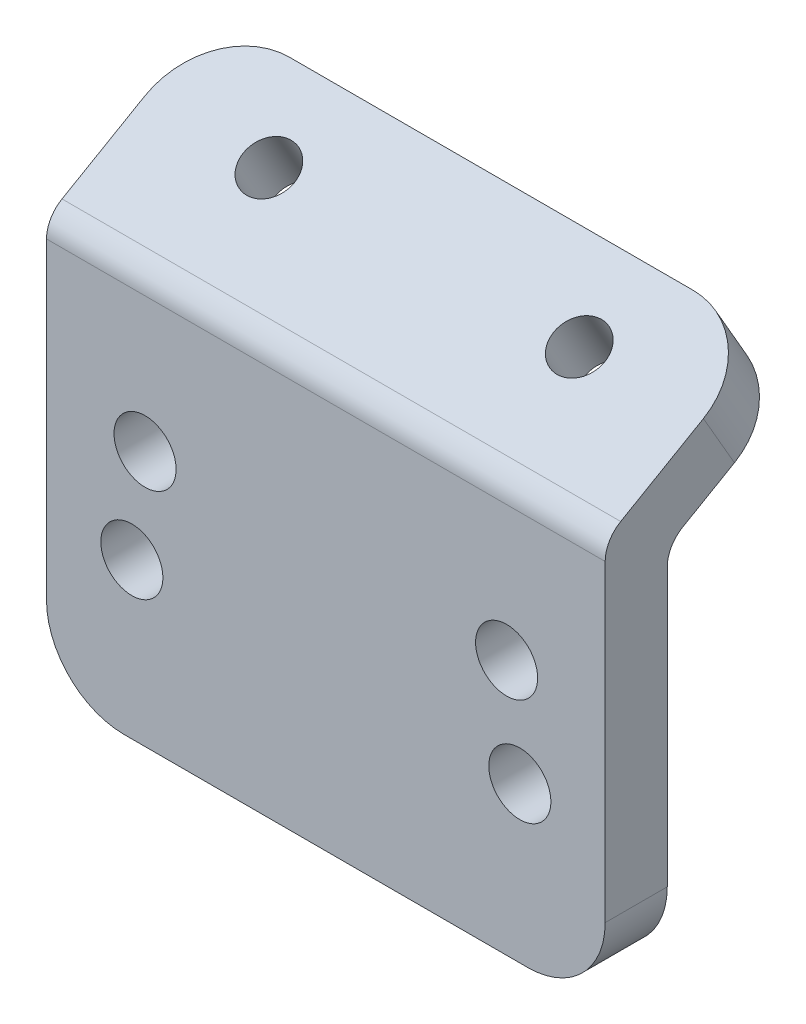
SolidWorks part; units mm, degrees
ref_plane "Plan de face" through (0, 0, 0) normal (0, 0, 1) x (1, 0, 0)
ref_plane "Plan de dessus" through (0, 0, 0) normal (0, 1, 0) x (1, 0, 0)
ref_plane "Plan de droite" through (0, 0, 0) normal (1, 0, 0) x (0, 0, -1)
sketch "Esquisse1" plane through (0, 0, 0) normal (0, 0, 1) x (1, 0, 0)
  line L1 (0, 0) -> (36, 0)
  line L2 (0, 0) -> (0, 24)
  line L3 (0, 24) -> (36, 24)
  line L4 (36, 0) -> (36, 24)
  dimension "D1" = 36
  dimension "D2" = 24
extrude "Boss.-Extru.1" add sketch "Esquisse1" along normal blind 4
sketch "Esquisse2" plane through (0, 0, 4) normal (0, 0, 1) x (1, 0, 0)
  line L0 (18, 0) -> (18, 24) construction
  line L1 (0, 0) -> (36, 0) construction
  line L2 (36, 24) -> (0, 24) construction
  line L3 (5.5, 10) -> (29.6481, 16.4705) construction
  line L4 (5.5, 10) -> (18, 10) construction
  circle A0 centre (5.5, 10) radius 2
  circle A1 centre (30.5, 10) radius 2
  circle A2 centre (29.6481, 16.4705) radius 2
  circle A3 centre (6.3519, 16.4705) radius 2
  dimension "D1" = 25
  dimension "D2" = 10
  dimension "D3" = 4
  dimension "D5" = 25
  dimension "D4" = 15
extrude "Enlèv. mat.-Extru.1" cut sketch "Esquisse2" against normal through all both and the other way through all
sketch "Esquisse3" plane through (36, 0, 0) normal (1, 0, 0) x (0, 0, -1)
  line L0 (0, 24) -> (8.6603, 29)
  line L1 (8.6603, 29) -> (6.6603, 32.4641)
  line L2 (6.6603, 32.4641) -> (-4, 26.3094)
  line L4 (-4, 26.3094) -> (-4, 24)
  line L5 (0, 0) -> (0, 24) construction
  line L6 (0, 24) -> (-4, 24)
  dimension "D1" = 4
  dimension "D2" = 10
  dimension "D3" = 120
extrude "Boss.-Extru.2" add sketch "Esquisse3" against normal up to vertex (36 mm away) up to point (0, 24, 0)
sketch "Esquisse4" plane through (0, 18, 10.3923) normal (0, -0.866, -0.5) x (1, 0, 0)
  line L0 (18, -22) -> (18, -15.2024) construction
  line L1 (0, -22) -> (36, -22) construction
  circle A0 centre (8, -17) radius 1.65
  circle A1 centre (28, -17) radius 1.65
  dimension "D2" = 3.3
  dimension "D3" = 5
  dimension "D1" = 10
extrude "Enlèv. mat.-Extru.2" cut sketch "Esquisse4" against normal through all both and the other way through all
fillet "Congé2" radius 5 4 edges at (0, 30.7321, -7.6603) (36, 30.7321, -7.6603) (0, 0, 2) (36, 0, 2)
fillet "Congé3" radius 2 2 edges at (18, 26.3094, 4) (18, 24, 0)
sketch "Esquisse5" [suppressed] plane through (0, 0, 4) normal (0, 0, 1) x (1, 0, 0)
  line L0 (5.5, 10) -> (29.6481, 16.4705) construction
  line L1 (3.0852, 9.353) -> (7.9148, 10.647) construction
  line L2 (2.5675, 11.2848) -> (7.3972, 12.5789)
  line L3 (3.6028, 7.4211) -> (8.4325, 8.7152)
  line L4 (17.5741, 13.2352) -> (17.1399, 14.8555) construction
  line L5 (32.063, 17.1175) -> (27.2333, 15.8234) construction
  line L6 (6.3519, 16.4705) -> (30.5, 10) construction
  line L7 (3.937, 17.1175) -> (8.7667, 15.8234) construction
  line L8 (4.4547, 19.0494) -> (9.2843, 17.7553)
  line L9 (3.4194, 15.1857) -> (8.249, 13.8916)
  line L10 (32.5806, 15.1857) -> (27.751, 13.8916)
  line L11 (31.5453, 19.0494) -> (26.7157, 17.7553)
  line L12 (32.9148, 9.353) -> (28.0852, 10.647) construction
  line L13 (32.3972, 7.4211) -> (27.5675, 8.7152)
  line L14 (33.4325, 11.2848) -> (28.6028, 12.5789)
  arc A0 (2.5675, 11.2848) -> (3.6028, 7.4211) centre (3.0852, 9.353) ccw
  arc A1 (8.4325, 8.7152) -> (7.3972, 12.5789) centre (7.9148, 10.647) ccw
  arc A2 (4.4547, 19.0494) -> (3.4194, 15.1857) centre (3.937, 17.1175) ccw
  arc A3 (8.249, 13.8916) -> (9.2843, 17.7553) centre (8.7667, 15.8234) ccw
  arc A4 (32.5806, 15.1857) -> (31.5453, 19.0494) centre (32.063, 17.1175) ccw
  arc A5 (26.7157, 17.7553) -> (27.751, 13.8916) centre (27.2333, 15.8234) ccw
  arc A6 (32.3972, 7.4211) -> (33.4325, 11.2848) centre (32.9148, 9.353) ccw
  arc A7 (28.6028, 12.5789) -> (27.5675, 8.7152) centre (28.0852, 10.647) ccw
  point P6 (5.5, 10)
  point P21 (6.3519, 16.4705)
  point P26 (29.6481, 16.4705)
  point P32 (30.5, 10)
  dimension "D1" = 4
  dimension "D2" = 5
extrude "Enlèv. mat.-Extru.3" [suppressed] cut sketch "Esquisse5" against normal through all both and the other way through all
